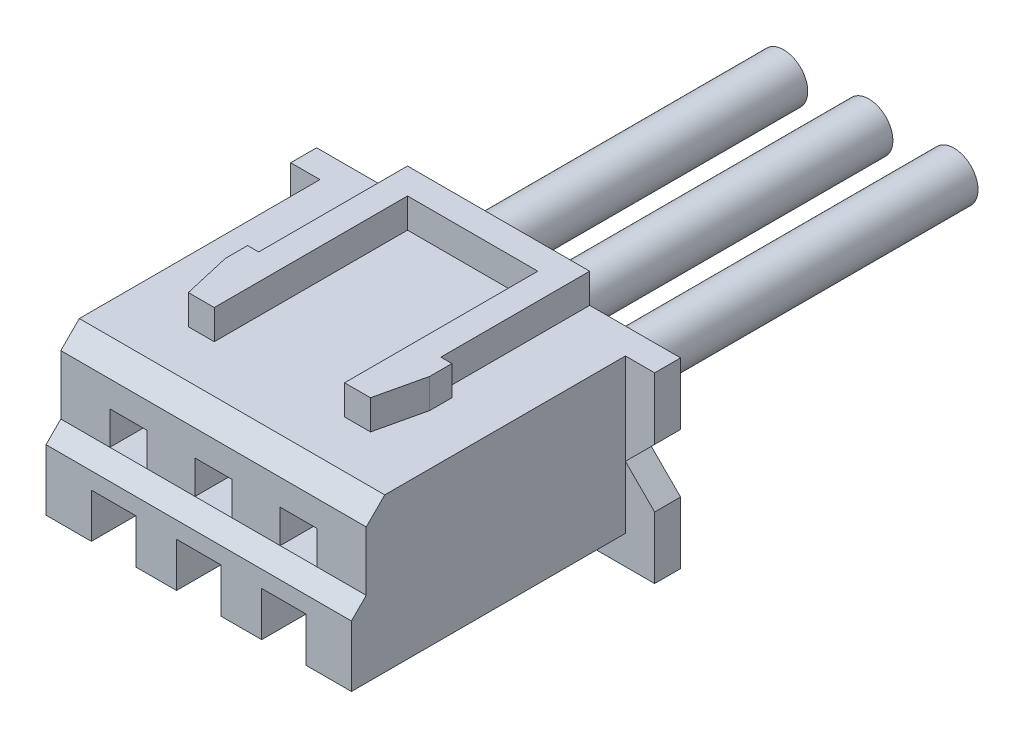
SolidWorks part; units mm, degrees
ref_plane "Plan de face" through (0, 0, 0) normal (0, 0, 1) x (1, 0, 0)
ref_plane "Plan de dessus" through (0, 0, 0) normal (0, 1, 0) x (1, 0, 0)
ref_plane "Plan de droite" through (0, 0, 0) normal (1, 0, 0) x (0, 0, -1)
sketch "Esquisse1" plane through (0, 0, 0) normal (0, 0, 1) x (1, 0, 0)
  line L0 (0, 0) -> (0, -2.5) construction
  line L1 (-4.125, 1.65) -> (4.125, 1.65)
  line L2 (-4.125, 1.65) -> (-4.125, -2.5)
  line L3 (-4.125, -2.5) -> (4.125, -2.5)
  line L4 (4.125, 1.65) -> (4.125, -2.5)
  line L5 (-0.5, 0.45) -> (0.5, -0.45) construction
  line L6 (-0.5, 0.45) -> (0.5, 0.45)
  line L7 (-0.5, 0.45) -> (-0.5, -0.45)
  line L8 (-0.5, -0.45) -> (0.5, -0.45)
  line L9 (0.5, 0.45) -> (0.5, -0.45)
  line L11 (-2.8, 0.45) -> (-1.8, 0.45)
  line L12 (-2.8, 0.45) -> (-2.8, -0.45)
  line L13 (-2.8, -0.45) -> (-1.8, -0.45)
  line L14 (-1.8, 0.45) -> (-1.8, -0.45)
  line L15 (1.8, 0.45) -> (2.8, 0.45)
  line L16 (1.8, 0.45) -> (1.8, -0.45)
  line L17 (1.8, -0.45) -> (2.8, -0.45)
  line L18 (2.8, 0.45) -> (2.8, -0.45)
  point P19 (-2.3, 0.45)
  dimension "D1" = 4.15
  dimension "D2" = 8.25
  dimension "D3" = 2.5
  dimension "D4" = 4.6
  dimension "D5" = 1
  dimension "D6" = 0.9
extrude "Boss.-Extru.1" add sketch "Esquisse1" against normal blind 8.1
sketch "Esquisse2" plane through (0, 0, -8.1) normal (0, 0, -1) x (-1, 0, 0)
  line L0 (0, 0) -> (0, 1.65) construction
  line L1 (-4.915, 1.65) -> (4.915, 1.65)
  line L2 (-4.915, 1.65) -> (-4.915, -0.025)
  line L3 (-4.915, -3.28) -> (4.915, -3.28)
  line L4 (4.915, 1.65) -> (4.915, -3.28)
  line L5 (-4.125, 1.65) -> (4.125, 1.65) construction
  line L6 (-4.915, -0.025) -> (-4.125, -0.815)
  line L7 (-2.8, 0.45) -> (2.8, 0.45)
  line L8 (-2.8, 0.45) -> (-2.8, -0.45)
  line L9 (-2.8, -0.45) -> (2.8, -0.45)
  line L10 (2.8, 0.45) -> (2.8, -0.45)
  line L11 (-4.125, -0.815) -> (-4.915, -1.605)
  line L12 (-4.915, -1.605) -> (-4.915, -3.28)
  line L13 (-4.125, -2.5) -> (-4.125, 1.65) construction
  dimension "D1" = 9.83
  dimension "D2" = 4.93
extrude "Boss.-Extru.2" add sketch "Esquisse2" against normal blind 0.7
sketch "Esquisse3" plane through (0, 0, -8.1) normal (0, 0, -1) x (-1, 0, 0)
  line L0 (0.5, -1.6) -> (0.95, -1.6)
  line L1 (-0.95, 1.05) -> (0.95, 1.05)
  line L2 (-0.95, 1.05) -> (-0.95, -1.6)
  line L3 (-0.95, -1.6) -> (-0.5, -1.6)
  line L4 (0.95, 1.05) -> (0.95, -1.6)
  line L5 (0, 0) -> (0, -1.9) construction
  line L6 (-0.5, -1.6) -> (-0.5, -1.9)
  line L7 (-0.5, -1.9) -> (0.5, -1.9)
  line L8 (0.5, -1.6) -> (0.5, -1.9)
  line L9 (-1.8, -1.6) -> (-1.35, -1.6)
  line L10 (-3.25, 1.05) -> (-1.35, 1.05)
  line L11 (-3.25, 1.05) -> (-3.25, -1.6)
  line L12 (-3.25, -1.6) -> (-2.8, -1.6)
  line L13 (-1.35, 1.05) -> (-1.35, -1.6)
  line L14 (2.8, -1.6) -> (3.25, -1.6)
  line L15 (-2.8, -1.6) -> (-2.8, -1.9)
  line L16 (-2.8, -1.9) -> (-1.8, -1.9)
  line L17 (-1.8, -1.6) -> (-1.8, -1.9)
  line L18 (1.35, 1.05) -> (3.25, 1.05)
  line L19 (1.35, 1.05) -> (1.35, -1.6)
  line L20 (1.35, -1.6) -> (1.8, -1.6)
  line L21 (3.25, 1.05) -> (3.25, -1.6)
  line L22 (-1.8, 0) -> (-0.5, 0) construction
  line L23 (1.8, -1.6) -> (1.8, -1.9)
  line L24 (1.8, -1.9) -> (2.8, -1.9)
  line L25 (2.8, -1.6) -> (2.8, -1.9)
  line L26 (-1.8, 0.45) -> (-1.8, -0.45) construction
  line L27 (-0.5, -0.45) -> (-0.5, 0.45) construction
  line L28 (-1.15, 0) -> (-1.15, -1.8822) construction
  line L29 (-4.915, 1.65) -> (4.915, 1.65) construction
  line L30 (4.125, -2.5) -> (-4.125, -2.5) construction
  dimension "D1" = 0.4
  dimension "D2" = 0.6
  dimension "D3" = 1
  dimension "D4" = 0.6
  dimension "D5" = 0.3
extrude "Enlèv. mat.-Extru.1" cut sketch "Esquisse3" against normal offset from surface (6.6 mm away) 1.5 up to face at (2.3, 0, 0)
sketch "Esquisse4" plane through (4.125, 0, 0) normal (1, 0, 0) x (0, 0, -1)
  line L0 (0, -0.85) -> (0.4, -0.45)
  line L1 (0, 1.65) -> (0.9, 1.65)
  line L2 (0, 1.65) -> (0, -0.85)
  line L4 (0.4, 1.15) -> (0.4, -0.45)
  line L5 (0.4, 1.15) -> (0.9, 1.65)
  line L6 (1.5, -0.45) -> (0, -0.45) construction
  dimension "D2" = 45
  dimension "D3" = 0.4
  dimension "D4" = 45
  dimension "D5" = 0.5
extrude "Enlèv. mat.-Extru.2" cut sketch "Esquisse4" against normal through all
sketch "Esquisse6" plane through (0, 0, 0) normal (0, 0, 1) x (1, 0, 0)
  line L0 (-4.125, -2.5) -> (4.125, -2.5) construction
  line L1 (-2.9, -1.3) -> (-1.7, -1.3)
  line L2 (-2.9, -1.3) -> (-2.9, -2.5)
  line L3 (-2.9, -2.5) -> (-1.7, -2.5)
  line L4 (-1.7, -1.3) -> (-1.7, -2.5)
  line L5 (0, 0) -> (0, -1.3) construction
  line L6 (-0.6, -1.3) -> (0.6, -1.3)
  line L7 (-0.6, -1.3) -> (-0.6, -2.5)
  line L8 (-0.6, -2.5) -> (0.6, -2.5)
  line L9 (0.6, -1.3) -> (0.6, -2.5)
  line L10 (1.7, -1.3) -> (2.9, -1.3)
  line L11 (1.7, -1.3) -> (1.7, -2.5)
  line L12 (1.7, -2.5) -> (2.9, -2.5)
  line L13 (2.9, -1.3) -> (2.9, -2.5)
  line L14 (-2.3, 0.45) -> (-2.3, -1.3) construction
  line L15 (-1.8, 0.45) -> (-2.8, 0.45) construction
  dimension "D1" = 1.2
  dimension "D2" = 1.2
extrude "Enlèv. mat.-Extru.3" cut sketch "Esquisse6" against normal blind 3.1
sketch "Esquisse7" plane through (0, 1.65, 0) normal (0, 1, 0) x (1, 0, 0)
  line L0 (4.915, 8.1) -> (-4.915, 8.1) construction
  line L1 (-2.46, 8.1) -> (2.46, 8.1)
  line L2 (-2.46, 8.1) -> (-2.46, 4.08)
  line L3 (-2.46, 2.18) -> (-1.76, 2.18)
  line L4 (2.46, 8.1) -> (2.46, 4.08)
  line L5 (1.76, 2.18) -> (2.46, 2.18)
  line L6 (-1.76, 7.4) -> (1.76, 7.4)
  line L7 (-1.76, 7.4) -> (-1.76, 2.18)
  line L8 (0, 0) -> (0, 11.4745) construction
  line L9 (1.76, 7.4) -> (1.76, 2.18)
  line L10 (-2.46, 2.18) -> (-2.76, 3.48)
  line L11 (-2.76, 3.48) -> (-2.76, 4.08)
  line L12 (-2.76, 4.08) -> (-2.46, 4.08)
  line L13 (2.46, 2.18) -> (2.76, 3.48)
  line L14 (2.76, 3.48) -> (2.76, 4.08)
  line L15 (2.76, 4.08) -> (2.46, 4.08)
  dimension "D1" = 4.92
  dimension "D2" = 0.7
  dimension "D3" = 0.7
  dimension "D4" = 5.92
  dimension "D5" = 1.9
  dimension "D6" = 1
  dimension "D7" = 0.6
extrude "Boss.-Extru.3" add sketch "Esquisse7" along normal blind 0.8
sketch "Esquisse8" plane through (0, 0, -8.1) normal (0, 0, -1) x (-1, 0, 0)
  line L0 (-2.3, 1.05) -> (-2.3, -0.4) construction
  line L1 (-1.35, 1.05) -> (-3.25, 1.05) construction
  line L2 (2.3, 1.05) -> (2.3, -0.4) construction
  line L3 (3.25, 1.05) -> (1.35, 1.05) construction
  line L4 (0, 1.05) -> (0, -0.4) construction
  line L5 (0.95, 1.05) -> (-0.95, 1.05) construction
  circle A0 centre (0, -0.4) radius 0.65
  circle A1 centre (-2.3, -0.4) radius 0.65
  circle A2 centre (2.3, -0.4) radius 0.65
  dimension "D1" = 1.3
  dimension "D2" = 0.4
extrude "Boss.-Extru.4" add sketch "Esquisse8" along normal blind 10 and the other way blind 2 separate body
